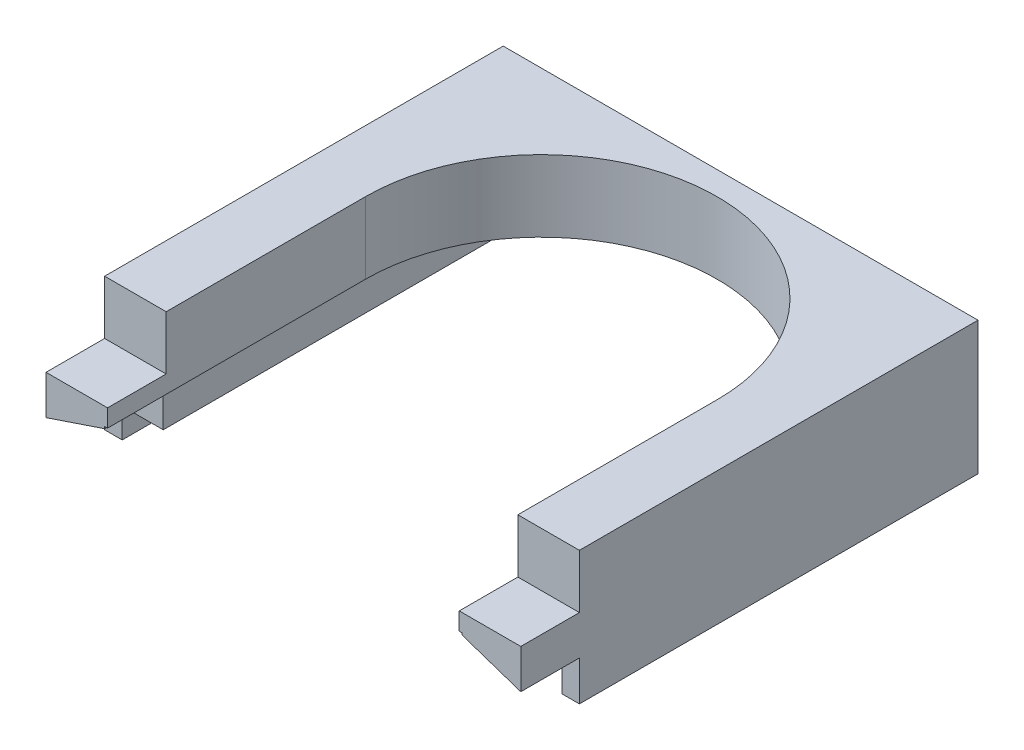
SolidWorks part; units mm, degrees
ref_plane "Plan de face" through (0, 0, 0) normal (0, 0, 1) x (1, 0, 0)
ref_plane "Plan de dessus" through (0, 0, 0) normal (0, 1, 0) x (1, 0, 0)
ref_plane "Plan de droite" through (0, 0, 0) normal (1, 0, 0) x (0, 0, -1)
sketch "Esquisse1" plane through (0, 0, 0) normal (0, 0, 1) x (1, 0, 0)
  line L1 (-32.5039, -5.5) -> (-32.5039, -10.5)
  line L2 (-32.5039, -10.5) -> (-35.5039, -10.5)
  line L3 (-35.5039, -10.5) -> (-35.5039, 12.2)
  line L4 (-35.5039, 12.2) -> (45.4961, 12.2)
  line L5 (45.4961, 12.2) -> (45.4961, -10.5)
  line L6 (45.4961, -10.5) -> (42.4961, -10.5)
  line L7 (42.4961, -10.5) -> (42.4961, -5.5)
  line L8 (-25.5039, -5.5) -> (-25.5039, 0)
  line L9 (-25.5039, 0) -> (35.4961, 0)
  line L10 (35.4961, 0) -> (35.4961, -5.5)
  line L11 (-32.5039, -5.5) -> (-25.5039, -5.5)
  line L12 (35.4961, -5.5) -> (42.4961, -5.5)
  dimension "D1" = 75
  dimension "D2" = 3
  dimension "D3" = 3
  dimension "D4" = 5
  dimension "D5" = 5
  dimension "D6" = 7
  dimension "D7" = 7
  dimension "D8" = 5.5
  dimension "D9" = 22.7
  dimension "D10" = 22.7
extrude "Boss.-Extru.1" add sketch "Esquisse1" along normal blind 68
sketch "Esquisse2" plane through (0, 12.2, 0) normal (0, 1, 0) x (1, 0, 0)
  line L0 (-35.5039, 0) -> (45.4961, -68) construction
  line L1 (-35.5039, -68) -> (45.4961, 0) construction
  line L2 (-25.0039, -34) -> (-25.0039, -68)
  line L3 (45.4961, -68) -> (-35.5039, -68) construction
  line L4 (-25.0039, -68) -> (34.9961, -68)
  line L5 (34.9961, -68) -> (34.9961, -34)
  arc A0 (34.9961, -34) -> (-25.0039, -34) centre (4.9961, -34) ccw
  dimension "D1" = 60
extrude "Enlèv. mat.-Extru.1" cut sketch "Esquisse2" against normal blind 30
sketch "Esquisse3" plane through (0, 0, 68) normal (0, 0, 1) x (1, 0, 0)
  line L6 (4.9961, 0) -> (4.9961, -9.7549) construction
  line L7 (-25.0039, 0) -> (34.9961, 0) construction
  line L13 (-35.5039, 12.2) -> (-35.5039, -10.5) construction
  line L14 (-35.5039, -3.7) -> (-35.5039, 3)
  line L15 (-35.5039, 3) -> (-25.0039, 3)
  line L16 (-25.0039, 0) -> (-25.0039, 12.2) construction
  line L17 (-25.0039, 3) -> (-25.0039, 0)
  line L18 (-25.0039, 0) -> (-25.5039, 0)
  line L24 (-35.5039, 12.2) -> (-35.5039, -10.5) construction
  line L25 (-35.5039, -3.7) -> (-25.5039, -0.3381)
  line L26 (-25.5039, -5.5) -> (-25.5039, 0) construction
  line L27 (-25.5039, -0.3381) -> (-25.5039, 0)
  line L28 (35.4961, -0.3381) -> (35.4961, 0)
  line L29 (45.4961, -3.7) -> (35.4961, -0.3381)
  line L30 (34.9961, 0) -> (35.4961, 0)
  line L31 (34.9961, 3) -> (34.9961, 0)
  line L32 (45.4961, 3) -> (34.9961, 3)
  line L33 (45.4961, -3.7) -> (45.4961, 3)
  dimension "D1" = 10.55
  dimension "D2" = 6.7
  dimension "D3" = 3
extrude "Boss.-Extru.2" add sketch "Esquisse3" along normal blind 10
